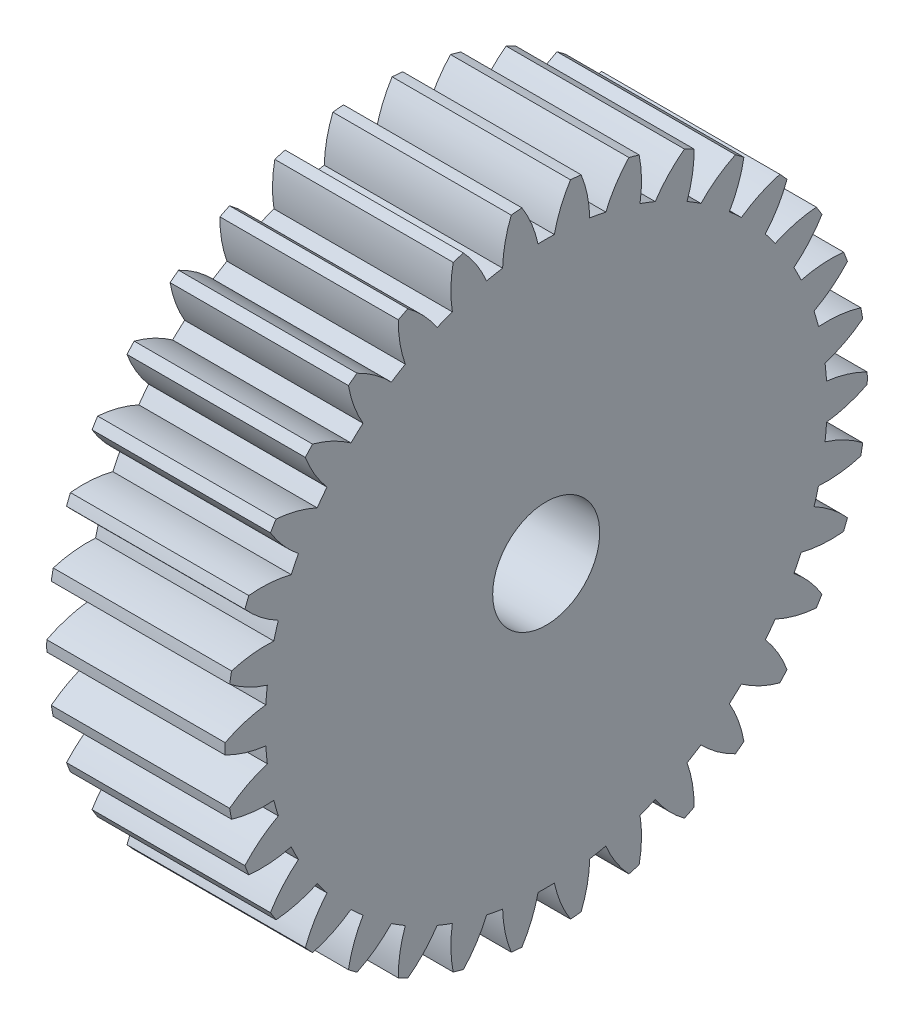
SolidWorks part; units mm, degrees
ref_plane "Plane1" through (0, 0, 0) normal (0, 0, 1) x (1, 0, 0)
ref_plane "Plane2" through (0, 0, 0) normal (0, 1, 0) x (1, 0, 0)
ref_plane "Plane3" through (0, 0, 0) normal (1, 0, 0) x (0, 0, -1)
other "Configuration Table"
sketch "HoldingSke" plane through (0, 0, 0) normal (0, 1, 0) x (1, 0, 0)
  line L0 (0, 0) -> (0.829, -0.5592)
  line L1 (-15, 0) -> (100, 0) construction
  line L2 (0, 0) -> (-2.1039, 2.3779)
  line L3 (0, 0) -> (-11.863, 4.5341)
  line L4 (0, 0) -> (7.1596, 4.8292)
  line L5 (0, 0) -> (-46.8476, -17.4728)
  line L6 (0, 0) -> (-8.2896, -5.593)
  line L7 (-2.1039, 2.3779) -> (8.6586, 51.2059)
  line L8 (-76.2, 54.61) -> (-75.2, 54.61)
  line L9 (-71.009, 38.7566) -> (-53.1078, 45.2721)
  line L10 (-76.2, 71.12) -> (104.1128, 71.12)
  line L11 (0, 0) -> (-10, 0)
  line L12 (-76.2, 101.6) -> (-76.162, 101.6)
  line L13 (24.9733, 27.94) -> (52.9518, 28.4284)
  line L14 (24.9733, 27.94) -> (24.9743, 27.94)
  line L15 (24.9733, 27.94) -> (100.4006, 29.5858)
  line L16 (-63.627, -1) -> (-12.827, -1)
  circle A0 centre (0, 0) radius 3
  circle A1 centre (0, 0) radius 15.749
  circle A2 centre (0, 0) radius 37.5
  circle A3 centre (0, 0) radius 3
  dimension "MHD" = 31.498
  dimension "Hub_dia" = 75
  dimension "Bore" = 6
  dimension "MBD" = 6
  dimension "Num_teeth" = 34
  dimension "Pitch" = 1
  dimension "Overall_len" = 50
  dimension "Show_teeth" = 34
  dimension "Thickness" = 10
  dimension "OAL" = 50.0001
  dimension "T_dim" = 1
  dimension "Ap" = 20
  dimension "H" = 19.05
  dimension "Pitch_radius" = 180.3128
  dimension "Width" = 10
  dimension "Backlash" = 0.038
  dimension "Addendum_fac" = 1
  dimension "Dedendum_fac" = 1.25
  dimension "Clearance_fac" = 0.25
  dimension "Dedendum_add" = 0.001
  dimension "Module" = 1
sketch "BasProSke" plane through (0, 0, 0) normal (0, 1, 0) x (1, 0, 0)
  line L0 (-10, 0) -> (60, 0) construction
  line L1 (0, 0) -> (0, 18)
  line L2 (0, 0) -> (10, 0)
  line L3 (10, 0) -> (10, 18)
  line L4 (10, 18) -> (0, 18)
  dimension "Thickness" = 10
  dimension "Diameter" = 36
revolve "Base-Revolve" add sketch "BasProSke" angle 360 about L0
sketch "TooCutSke" plane through (0, 0, 0) normal (1, 0, 0) x (0, 0, -1)
  line L1 (0, 0) -> (0, 107) construction
  line L2 (0, 0) -> (-0.8516, 16.9787) construction
  line L3 (0, 0) -> (-3.1343, 33.8247) construction
  line L4 (-0.8516, 16.9787) -> (-1.5672, 16.9124) construction
  arc A0 (0.4581, 15.7423) -> (-0.4581, 15.7423) centre (0, 0) ccw
  arc A1 (1.3773, 17.9727) -> (-1.3773, 17.9727) centre (0, 0) ccw
  circle A2 centre (0, 0) radius 17 construction
  circle A3 centre (0, 0) radius 15.9748 construction
  arc A4 (-0.4581, 15.7423) -> (-1.3773, 17.9727) centre (-7.1051, 14.3077) ccw
  arc A5 (1.3773, 17.9727) -> (0.4581, 15.7423) centre (7.1051, 14.3077) ccw
  dimension "Root_dia" = 31.498
  dimension "Overcut_dia" = 36.0508
  dimension "Pitch_dia" = 34
  dimension "Base_dia" = 31.9495
  dimension "Flank_rad" = 6.8
  dimension "Half_ang" = 5.294
  dimension "Half_CT" = 0.7186
extrude "ToothCut" cut sketch "TooCutSke" along normal through all
fillet "Breaks" [suppressed] radius 0.02
fillet "RootFillets" [suppressed] radius 0.251
pattern_circular "TeethCuts" count 34 every 10.588 about axis through (-10, 0, 0) along (1, 0, 0) of "ToothCut", "RootFillets", "Breaks"
sketch "HubNeaOneSke" plane through (0, 0, 0) normal (-1, 0, 0) x (0, 0, 1)
  circle A0 centre (0, 0) radius 15.749
  dimension "Diameter" = 31.498
extrude "HubNearOne" [suppressed] add sketch "HubNeaOneSke" along normal blind 40.0001
sketch "HubNeaBotSke" plane through (0, 0, 0) normal (-1, 0, 0) x (0, 0, 1)
  circle A0 centre (0, 0) radius 15.749
  dimension "Diameter" = 31.498
extrude "HubNearBoth" [suppressed] add sketch "HubNeaBotSke" along normal blind 20
ref_plane "FarPln" through (10, 0, 0) normal (1, 0, 0) x (0, 0, -1)
sketch "HubFarSke" plane through (10, 0, 0) normal (1, 0, 0) x (0, 0, -1)
  circle A0 centre (0, 0) radius 15.749
  dimension "Diameter" = 31.498
extrude "HubFar" [suppressed] add sketch "HubFarSke" along normal blind 20
sketch "BorSke" plane through (0, 0, 0) normal (1, 0, 0) x (0, 0, -1)
  circle A0 centre (0, 0) radius 3
  dimension "Diameter" = 6
extrude "Bore" cut sketch "BorSke" along normal mid plane 100.0001
sketch "KeySke" plane through (0, 0, 0) normal (1, 0, 0) x (0, 0, -1)
  line L0 (-1, 0) -> (-1, 4)
  line L1 (-1, 4) -> (1, 4)
  line L2 (1, 4) -> (1, 0)
  line L3 (0, 0) -> (0, 34) construction
  line L4 (-1, 0) -> (1, 0)
  dimension "Offset" = 4
  dimension "Width" = 2
extrude "Keyway" [suppressed] cut sketch "KeySke" along normal mid plane 100.0001
pattern_circular "Keyway2" [suppressed] count 2 every 90 about axis through (-10, 0, 0) along (1, 0, 0)
equation "' \"Module@HoldingSke\" = 6.35"
equation "' \"Num_teeth@HoldingSke\" = 12"
equation "' \"Ap@HoldingSke\" =  20"
equation "' \"Ap@HoldingSke\" = 20"
equation "' \"Width@HoldingSke\" = 0.5 * 25.4"
equation "' \"Hub_dia@HoldingSke\"= 1 * 25.4"
equation "' \"Hub_dia@HoldingSke\" = 1 * 25.4"
equation "' \"Overall_len@HoldingSke\" = 1.0 * 25.4"
equation "' \"Bore@HoldingSke\" = 0.75 * 25.4"
equation "' \"T_dim@HoldingSke\" = 0.1 * 25.4"
equation "' \"Width@KeySke\" = 0.25 * 25.4"
equation "' \"Show_teeth@HoldingSke\" = 13"
equation "' \"Backlash@HoldingSke\" = 0.009 * 25.4"
equation "' \"Addendum_fac@HoldingSke\" = 1.0"
equation "' \"Dedendum_fac@HoldingSke\" = 1.25"
equation "' \"Dedendum_add@HoldingSke\" = 0.00005 * 25.4"
equation "' \"Clearance_fac@HoldingSke\" = 0.25"
equation "\"Pitch@HoldingSke\" = 1 / \"Module@HoldingSke\""
equation "\"Overcut_dia@TooCutSke\" = (\"Num_teeth@HoldingSke\" + 2 * \"Addendum_fac@HoldingSke\") / \"Pitch@HoldingSke\" + 0.002 * 25.4"
equation "\"Pitch_dia@TooCutSke\" = \"Num_teeth@HoldingSke\" / \"Pitch@HoldingSke\""
equation "\"Base_dia@TooCutSke\" = \"Num_teeth@HoldingSke\" / \"Pitch@HoldingSke\" * cos((\"Ap@HoldingSke\"  * 3.14159265 / 180))"
equation "\"Root_dia@TooCutSke\" = (\"Num_teeth@HoldingSke\" + 2) / \"Pitch@HoldingSke\" - 2 * (\"Addendum_fac@HoldingSke\" + \"Dedendum_fac@HoldingSke\") / \"Pitch@HoldingSke\" - \"Dedendum_add@HoldingSke\" * 2"
equation "\"Half_ang@TooCutSke\" = 180 / \"Num_teeth@HoldingSke\""
equation "\"Half_CT@TooCutSke\" = \"Num_teeth@HoldingSke\" / \"Pitch@HoldingSke\" * sin((3.14159265 / 2 / \"Num_teeth@HoldingSke\")) / 2 - 7 * \"Backlash@HoldingSke\" / 4"
equation "\"Flank_rad@TooCutSke\" = \"Num_teeth@HoldingSke\" / \"Pitch@HoldingSke\" / 5"
equation "\"Radius@RootFillets\" = \"Clearance_fac@HoldingSke\" / \"Pitch@HoldingSke\" + \"Dedendum_add@HoldingSke\""
equation "\"Break_rad@Breaks\" = 0.02 / \"Pitch@HoldingSke\""
equation "\"Thickness@HoldingSke\" = \"Width@HoldingSke\""
equation "\"OAL@HoldingSke\" = \"Thickness@HoldingSke\""
equation "\"MHD@HoldingSke\" = (\"Num_teeth@HoldingSke\" + 2) / \"Pitch@HoldingSke\" - 2 * (\"Addendum_fac@HoldingSke\" + \"Dedendum_fac@HoldingSke\")  / \"Pitch@HoldingSke\" - \"Dedendum_add@HoldingSke\" * 2"
equation "\"MBD@HoldingSke\" = (\"Num_teeth@HoldingSke\" + 2) / \"Pitch@HoldingSke\" - 2 * (\"Addendum_fac@HoldingSke\" + \"Dedendum_fac@HoldingSke\")  / \"Pitch@HoldingSke\" - \"Dedendum_add@HoldingSke\" * 2 - 0.002 * 25.4"
equation "\"MHD@HoldingSke\" = ((sgn( \"MHD@HoldingSke\" - \"Hub_dia@HoldingSke\" )-1)*( \"MHD@HoldingSke\" - \"Hub_dia@HoldingSke\" ))/-2+ \"Hub_dia@HoldingSke\""
equation "\"MBD@HoldingSke\" = ((sgn( \"MBD@HoldingSke\" - \"Bore@HoldingSke\" )-1)*( \"MBD@HoldingSke\" - \"Bore@HoldingSke\" ))/-2+ \"Bore@HoldingSke\""
equation "\"OAL@HoldingSke\" = ((sgn( \"OAL@HoldingSke\" - \"Overall_len@HoldingSke\" )+1)*( \"OAL@HoldingSke\" - \"Overall_len@HoldingSke\" ))/2 + \"Overall_len@HoldingSke\" + 0.000002 * 25.4"
equation "\"Num_teeth@TeethCuts\" = int( \"Show_teeth@HoldingSke\" ) + 1"
equation "\"Num_teeth@TeethCuts\" = ((sgn( \"Num_teeth@TeethCuts\" - \"Num_teeth@HoldingSke\" )-1)*( \"Num_teeth@TeethCuts\" - \"Num_teeth@HoldingSke\" ))/-2+ \"Num_teeth@HoldingSke\""
equation "\"Num_teeth@TeethCuts\" = ((sgn( \"Num_teeth@TeethCuts\" - 2.0)+1)*( \"Num_teeth@TeethCuts\" - 2.0))/2 +2.0"
equation "\"Angle@TeethCuts\" = 360.0 / \"Num_teeth@HoldingSke\""
equation "\"Diameter@BasProSke\" = (\"Num_teeth@HoldingSke\" + 2 * \"Addendum_fac@HoldingSke\") / \"Pitch@HoldingSke\""
equation "\"Thickness@BasProSke\"  = \"Thickness@HoldingSke\""
equation "' \"Fillet_rad@BasProSke\" =  \"Thickness@HoldingSke\" * 0.05"
equation "' \"Fillet_rad@BasProSke\" = \"Thickness@HoldingSke\" * 0.05"
equation "\"MHD@HoldingSke\" = ((sgn( \"MHD@HoldingSke\" - \"Root_dia@TooCutSke\" )-1)*( \"MHD@HoldingSke\" - \"Root_dia@TooCutSke\" ))/-2+ \"Root_dia@TooCutSke\""
equation "\"Diameter@HubNeaOneSke\" = \"MHD@HoldingSke\""
equation "\"Length@HubNearOne\" = \"OAL@HoldingSke\" - \"Thickness@BasProSke\""
equation "\"Diameter@HubNeaBotSke\" = \"MHD@HoldingSke\""
equation "\"Length@HubNearBoth\" = ( \"OAL@HoldingSke\" - \"Thickness@BasProSke\" ) / 2.0"
equation "\"Thickness@FarPln\" = \"Thickness@BasProSke\""
equation "\"Diameter@HubFarSke\" = \"MHD@HoldingSke\""
equation "\"Length@HubFar\" = ( \"OAL@HoldingSke\" - \"Thickness@BasProSke\" ) / 2.0"
equation "\"Diameter@BorSke\" = \"MBD@HoldingSke\""
equation "\"D1@Bore\" = \"OAL@HoldingSke\" * 2.0"
equation "\"D1@Keyway\" = \"OAL@HoldingSke\" * 2.0"
equation "\"Offset@KeySke\" = \"T_dim@HoldingSke\" + \"MBD@HoldingSke\" / 2.0"
